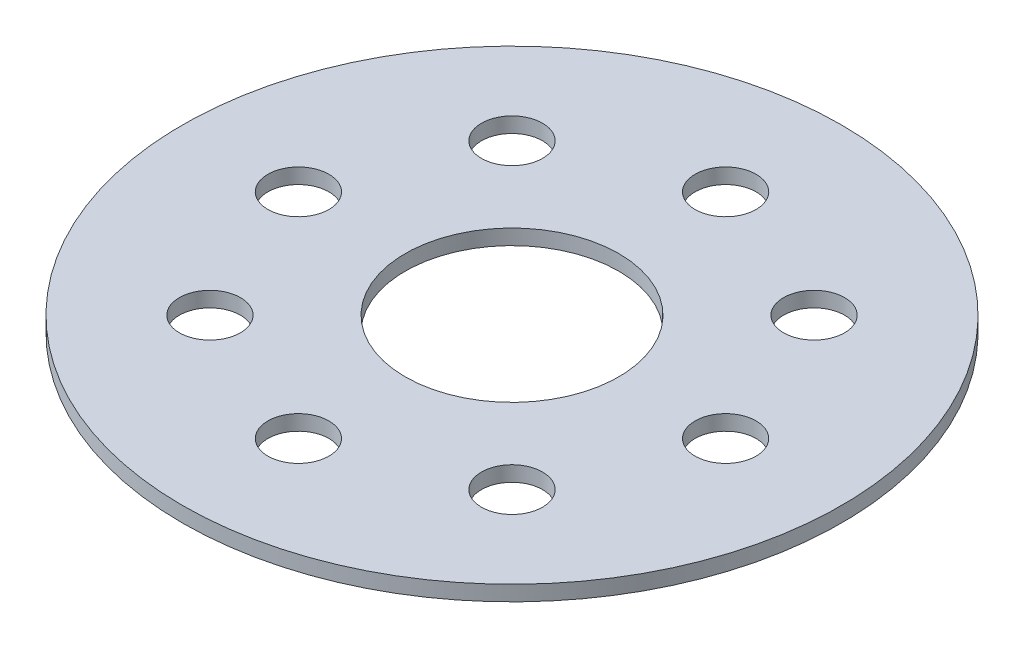
SolidWorks part; units mm, degrees
ref_plane "Front Plane" through (0, 0, 0) normal (0, 0, 1) x (1, 0, 0)
ref_plane "Top Plane" through (0, 0, 0) normal (0, 1, 0) x (1, 0, 0)
ref_plane "Right Plane" through (0, 0, 0) normal (1, 0, 0) x (0, 0, -1)
sketch "Sketch1" plane through (0, 0, 0) normal (0, 1, 0) x (1, 0, 0)
  circle A0 centre (0, 0) radius 68.58
  circle A1 centre (0, 0) radius 22.225
  dimension "D1" = 137.16
  dimension "D2" = 44.45
extrude "Boss-Extrude1" add sketch "Sketch1" along normal blind 3.175
sketch "Sketch2" plane through (0, 3.175, 0) normal (0, 1, 0) x (1, 0, 0)
  circle A0 centre (0, 44.45) radius 6.35
  dimension "D1" = 44.45
extrude "Cut-Extrude1" cut sketch "Sketch2" against normal blind 3.175
pattern_circular "CirPattern1" count 8 over 360 about axis through (0, 0, 0) along (0, 1, 0) of "Cut-Extrude1"
